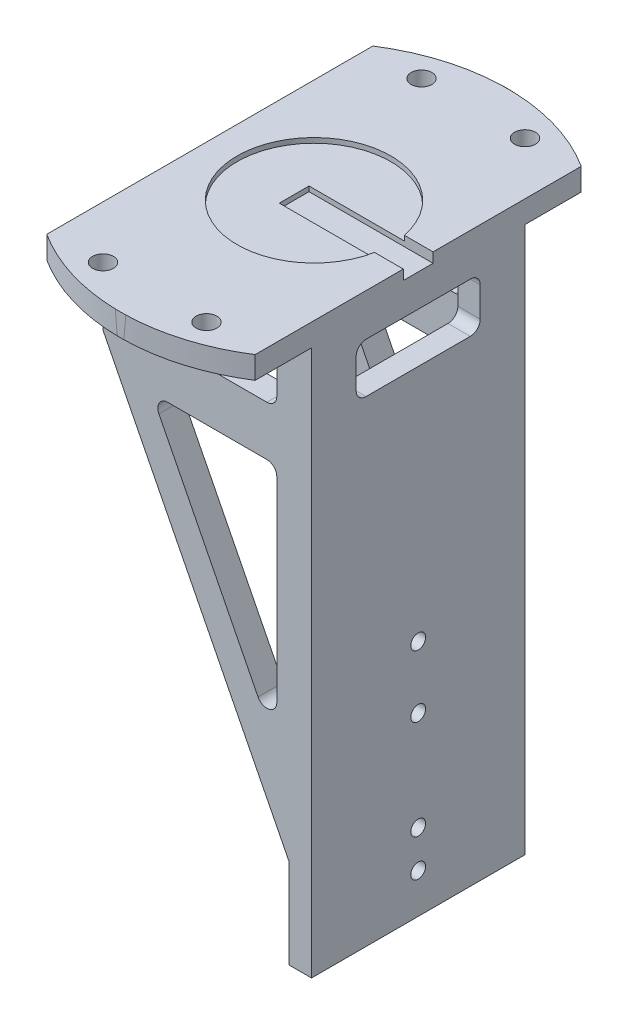
SolidWorks part; units mm, degrees
ref_plane "Front Plane" through (0, 0, 0) normal (0, 0, 1) x (1, 0, 0)
ref_plane "Top Plane" through (0, 0, 0) normal (0, 1, 0) x (1, 0, 0)
ref_plane "Right Plane" through (0, 0, 0) normal (1, 0, 0) x (0, 0, -1)
other "Graphic1"
other "Graphic (Closed) -1"
sketch "Sketch1" plane through (0, 0, 0) normal (0, 0, 1) x (1, 0, 0)
  line L0 (0, 114.5) -> (42, 114.5)
  line L1 (42, 114.5) -> (42, 0)
  line L2 (42, 0) -> (37.5, 0)
  line L3 (37.5, 0) -> (37.5, 18)
  line L4 (37.5, 18) -> (0, 92)
  line L5 (0, 92) -> (0, 114.5)
extrude "Boss-Extrude1" add sketch "Sketch1" along normal blind 80
sketch "Sketch2" plane through (0, 0, 0) normal (1, 0, 0) x (0, 0, -1)
  line L0 (-22.5, 110) -> (-55.5, 110)
  line L1 (-55.5, 110) -> (-55.5, 0)
  line L2 (-55.5, 0) -> (-22.5, 0)
  line L3 (-22.5, 0) -> (-22.5, 110)
extrude "Cut-Extrude2" cut sketch "Sketch2" along normal blind 37.5
sketch "Sketch6" plane through (0, 0, 0) normal (1, 0, 0) x (0, 0, -1)
  line L0 (-17.5, 110) -> (-0.0119, 110)
  line L1 (-0.0119, 110) -> (-0.0119, 114.4998)
  line L2 (-0.0119, 114.4998) -> (14.0049, 114.4998)
  line L3 (-17.5, 110) -> (-17.5, 0)
  line L6 (-17.5, 0) -> (14.0049, 0)
  line L7 (14.0049, 114.4998) -> (14.0049, 0)
  line L8 (-60.5, 110) -> (-77.9949, 110)
  line L9 (-77.9949, 110) -> (-77.9857, 114.5)
  line L10 (-77.9857, 114.5) -> (-108.5932, 114.5)
  line L11 (-108.5932, 114.5) -> (-108.5932, 0)
  line L12 (-60.5, 0) -> (-108.5932, 0)
  line L13 (-60.5, 110) -> (-60.5, 0)
extrude "Cut-Extrude6" cut sketch "Sketch6" along normal blind 55.5
sketch "Sketch7" plane through (0, 0, 0) normal (1, 0, 0) x (0, 0, -1)
  line L0 (-49.5, 106) -> (-28.1871, 105.9754)
  line L1 (-26.5, 104) -> (-26.5, 98)
  line L2 (-28.5, 96) -> (-49.5, 96)
  line L3 (-51.5, 98) -> (-51.5, 104)
  arc A0 (-28.1871, 105.9754) -> (-26.5, 104) centre (-28.5, 104) cw
  arc A1 (-26.5, 98) -> (-28.5, 96) centre (-28.5, 98) cw
  arc A2 (-49.5, 96) -> (-51.5, 98) centre (-49.5, 98) cw
  arc A3 (-51.5, 104) -> (-49.5, 106) centre (-49.5, 104) cw
  circle A4 centre (-39, 48) radius 1.5
  circle A5 centre (-39, 35.5) radius 1.5
  circle A6 centre (-39, 8) radius 1.5
  circle A7 centre (-39, 15.5) radius 1.5
extrude "Cut-Extrude8" cut sketch "Sketch7" against normal blind 55.5 and the other way through all
sketch "Sketch8" plane through (0, 0, 0) normal (0, 0, 1) x (1, 0, 0)
  line L0 (33, 86) -> (13.0226, 86)
  line L1 (35, 84) -> (35, 44.578)
  line L2 (11.2386, 83.0959) -> (31.216, 43.6739)
  line L3 (9, 106) -> (33, 106)
  line L4 (9, 96) -> (33, 96)
  line L5 (7, 104) -> (7, 98)
  line L6 (35, 104) -> (35, 98)
  arc A0 (11.2386, 83.0959) -> (13.0226, 86) centre (13.0226, 84) cw
  arc A1 (33, 86) -> (35, 84) centre (33, 84) cw
  arc A2 (31.216, 43.6739) -> (35, 44.578) centre (33, 44.578) ccw
  arc A3 (33, 96) -> (35, 98) centre (33, 98) ccw
  arc A4 (33, 106) -> (35, 104) centre (33, 104) cw
  arc A5 (7, 98) -> (9, 96) centre (9, 98) ccw
  arc A6 (7, 104) -> (9, 106) centre (9, 104) cw
extrude "Cut-Extrude9" cut sketch "Sketch8" along normal blind 110.5
sketch "Sketch10" plane through (0, 0, 0) normal (0, 1, 0) x (1, 0, 0)
  line L0 (0, -6.1366) -> (0, 15.4695)
  line L1 (0, 15.4695) -> (11.3396, 15.4695)
  line L2 (42, -6.1366) -> (42, 15.4695)
  line L3 (42, 15.4695) -> (11.3396, 15.4695)
  line L4 (0, -71.8633) -> (0, -99.2754)
  line L5 (0, -99.2754) -> (42, -99.2754)
  line L6 (42, -99.2754) -> (42, -71.8633)
  arc A0 (0, -6.1366) -> (42, -6.1366) centre (21, -39) cw
  arc A1 (0, -71.8633) -> (42, -71.8633) centre (21, -39) ccw
extrude "Cut-Extrude10" cut sketch "Sketch10" along normal blind 196.5
sketch "Sketch11" plane through (0, 0, 0) normal (0, 1, 0) x (1, 0, 0)
  circle A0 centre (10.5707, -6.9018) radius 2.1
  circle A1 centre (31.4293, -6.9018) radius 2.1
  circle A2 centre (31.4293, -71.0982) radius 2.1
  circle A3 centre (10.5707, -71.0982) radius 2.1
extrude "Cut-Extrude11" cut sketch "Sketch11" along normal blind 196.5
sketch "Sketch12" plane through (0, 0, 0) normal (0, 1, 0) x (1, 0, 0)
  circle A0 centre (21, -39) radius 15.5
extrude "Cut-Extrude12" cut sketch "Sketch12" against normal blind 1 from offset 114.5
sketch "Sketch13" plane through (0, 0, 0) normal (0, 1, 0) x (1, 0, 0)
  line L0 (42, -36) -> (17, -36)
  line L1 (17, -36) -> (17, -42)
  line L2 (17, -42) -> (42, -42)
  line L3 (42, -42) -> (42, -36)
extrude "Cut-Extrude13" cut sketch "Sketch13" against normal blind 2 from offset 114.5
